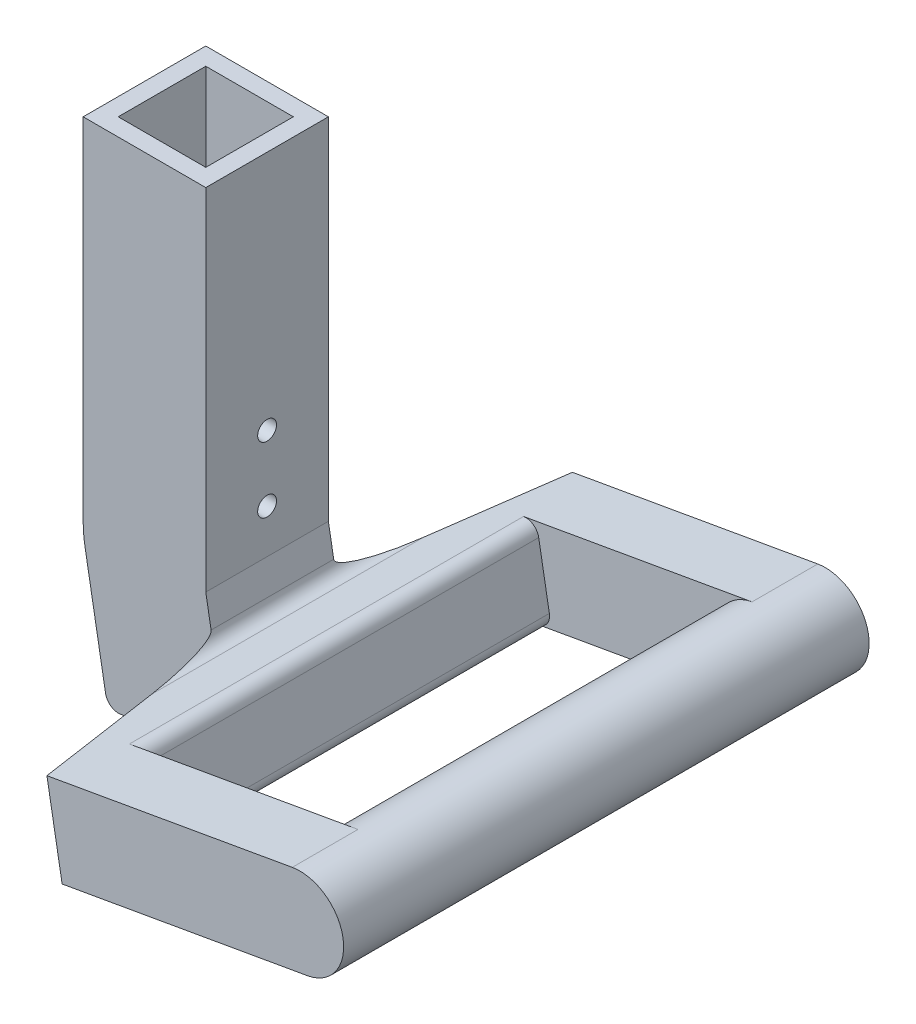
SolidWorks part; units mm, degrees
ref_plane "Front Plane" through (0, 0, 0) normal (0, 0, 1) x (1, 0, 0)
ref_plane "Top Plane" through (0, 0, 0) normal (0, 1, 0) x (1, 0, 0)
ref_plane "Right Plane" through (0, 0, 0) normal (1, 0, 0) x (0, 0, -1)
sketch "Sketch1" plane through (0, 0, 0) normal (0, 1, 0) x (1, 0, 0)
  line L0 (-4, 24) -> (24, 24)
  line L1 (0, 0) -> (20, 0)
  line L2 (0, 0) -> (0, 20)
  line L3 (0, 20) -> (20, 20)
  line L4 (20, 0) -> (20, 20)
  line L5 (24, -4) -> (24, 24)
  line L6 (-4, -4) -> (24, -4)
  line L7 (-4, -4) -> (-4, 24)
  dimension "D1" = 20
  dimension "D2" = 4
extrude "Boss-Extrude1" add sketch "Sketch1" along normal blind 30
sketch "Sketch2" plane through (0, 0, 0) normal (0, -1, 0) x (1, 0, 0)
  line L1 (-4, 4) -> (24, 4)
  line L2 (-4, 4) -> (-4, -24)
  line L3 (-4, -24) -> (24, -24)
  line L4 (24, 4) -> (24, -24)
extrude "Boss-Extrude2" add sketch "Sketch2" against normal blind 3
sketch "Sketch3" plane through (24, 0, 0) normal (1, 0, 0) x (0, 0, -1)
  line L0 (-4, 0) -> (24, 0) construction
  line L1 (-4, 30) -> (-4, 0) construction
  circle A0 centre (10, 25) radius 2.15
  circle A1 centre (10, 10) radius 2.15
  dimension "D1" = 4.3
  dimension "D2" = 15
  dimension "D3" = 10
  dimension "D4" = 14
extrude "Cut-Extrude1" cut sketch "Sketch3" against normal through all
sketch "Sketch4" plane through (0, 0, 4) normal (0, 0, 1) x (1, 0, 0)
  line L0 (24, 0) -> (29.2094, -29.5442)
  line L1 (29.2094, -29.5442) -> (1.6348, -34.4064)
  line L2 (1.6348, -34.4064) -> (-3.5746, -4.8621)
  line L3 (24, 30) -> (24, 0) construction
  line L4 (-4, 0) -> (24, 0) construction
  line L5 (-4, 0) -> (24, 0)
  arc A0 (-4, 0) -> (-3.5746, -4.8621) centre (24, 0) ccw
  dimension "D1" = 170
  dimension "D2" = 30
extrude "Boss-Extrude3" add sketch "Sketch4" against normal up to surface (28 mm away) up to face at (10, 15, -24)
sketch "Sketch5" plane through (5.9331, -33.6485, 0) normal (0.1736, -0.9848, 0) x (0, 0, -1)
  line L0 (24, 23.6354) -> (-4, 23.6354)
  line L1 (-4, 23.6354) -> (-50, 31.7464)
  line L2 (-50, 31.7464) -> (-50, 88.6354)
  line L3 (-50, 88.6354) -> (-35, 88.6354)
  line L4 (70, 88.6354) -> (70, 31.7464)
  line L5 (70, 31.7464) -> (24, 23.6354)
  line L6 (-35, 88.6354) -> (-35, 38.6354)
  line L7 (-35, 38.6354) -> (55, 38.6354)
  line L8 (55, 38.6354) -> (55, 88.6354)
  line L9 (55, 88.6354) -> (70, 88.6354)
  line L12 (-4, -4.3646) -> (-4, 23.6354) construction
  dimension "D1" = 120
  dimension "D2" = 50
  dimension "D3" = 15
  dimension "D4" = 100
  dimension "D5" = 15
extrude "Boss-Extrude4" add sketch "Sketch5" against normal blind 20
sketch "Sketch6" plane through (0, 0, -55) normal (0, 0, 1) x (1, 0, 0)
  line L0 (89.749, 1.4391) -> (93.2219, -18.2571) construction
  circle A0 centre (91.4855, -8.409) radius 10
extrude "Boss-Extrude5" add sketch "Sketch6" along normal up to surface and the other way up to surface up to face at (63.4731, -13.3484, 50) other way up to face at (63.4731, -13.3484, -70)
sketch "Sketch7" plane through (0, 30, 0) normal (0, 1, 0) x (1, 0, 0)
  line L0 (20, 0) -> (20, 20) construction
  line L1 (0, 0) -> (20, 0) construction
  line L2 (0, 20) -> (0, 0) construction
  line L3 (20, 20) -> (0, 20) construction
  line L4 (-4, 24) -> (-4, -4)
  line L5 (-4, -4) -> (24, -4)
  line L6 (24, -4) -> (24, 24)
  line L7 (24, 24) -> (-4, 24)
  line L8 (-4, 24) -> (-4, -4)
  line L9 (-4, -4) -> (24, -4)
  line L10 (24, -4) -> (24, 24)
  line L11 (24, 24) -> (-4, 24)
  line L12 (20, 0) -> (20, 20)
  line L13 (0, 0) -> (20, 0)
  line L14 (0, 20) -> (0, 0)
  line L15 (20, 20) -> (0, 20)
  dimension "D1" = 0
extrude "Boss-Extrude6" add sketch "Sketch7" along normal blind 50
fillet "Fillet1" radius 3 4 edges at (43.9816, -26.9395, -10) (40.5086, -7.2434, -10) (25.7365, -9.8481, -10) (1.6348, -34.4064, -10)
